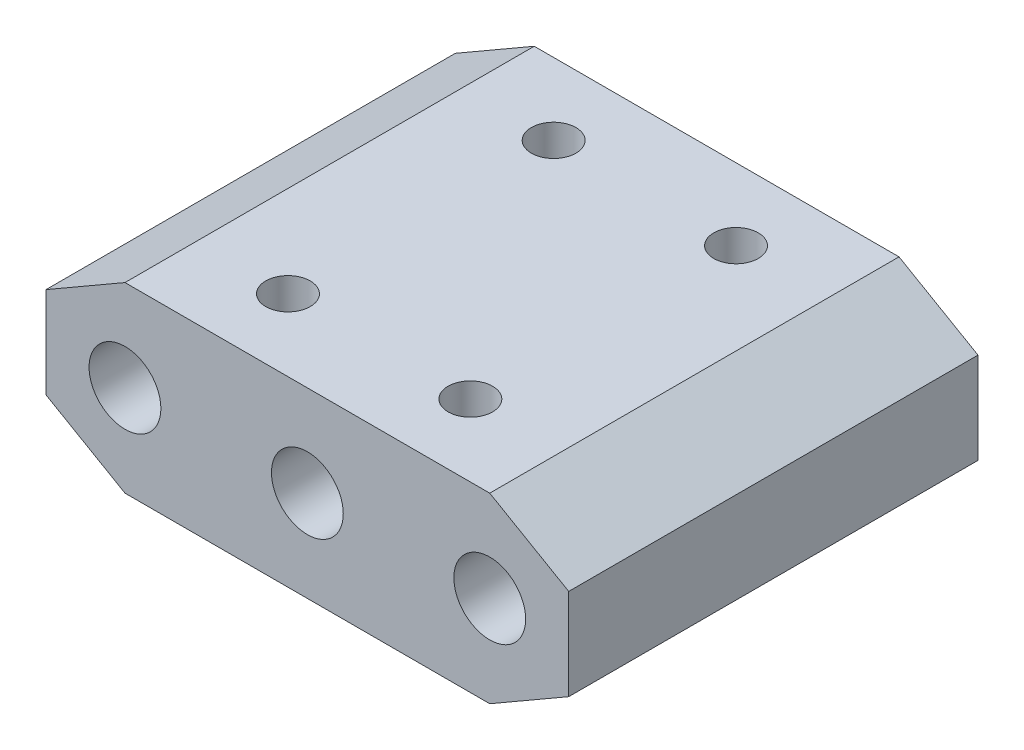
SolidWorks part; units mm, degrees
material "6061-T6 (SS)"
ref_plane "Front Plane" through (0, 0, 0) normal (0, 0, 1) x (1, 0, 0)
ref_plane "Top Plane" through (0, 0, 0) normal (0, 1, 0) x (1, 0, 0)
ref_plane "Right Plane" through (0, 0, 0) normal (1, 0, 0) x (0, 0, -1)
sketch "Sketch1" plane through (0, 0, 0) normal (0, 0, 1) x (1, 0, 0)
  line L0 (0, 6.35) -> (6.35, 6.35) construction
  line L1 (0, 0) -> (38.1, 0)
  line L2 (0, 0) -> (0, 12.7)
  line L3 (0, 12.7) -> (38.1, 12.7)
  line L4 (38.1, 0) -> (38.1, 12.7)
  line L5 (6.35, 6.35) -> (19.05, 6.35) construction
  line L6 (19.05, 6.35) -> (31.75, 6.35) construction
  line L7 (31.75, 6.35) -> (38.1, 6.35) construction
  line L9 (6.35, 0) -> (11.8493, 3.175)
  line L10 (11.8493, 3.175) -> (11.8493, 9.525)
  line L11 (11.8493, 9.525) -> (6.35, 12.7)
  line L12 (6.35, 12.7) -> (0.8507, 9.525)
  line L13 (0.8507, 9.525) -> (0.8507, 3.175)
  line L14 (0.8507, 3.175) -> (6.35, 0)
  line L15 (31.75, 0) -> (37.2493, 3.175)
  line L16 (37.2493, 3.175) -> (37.2493, 9.525)
  line L17 (37.2493, 9.525) -> (31.75, 12.7)
  line L18 (31.75, 12.7) -> (26.2507, 9.525)
  line L19 (26.2507, 9.525) -> (26.2507, 3.175)
  line L20 (26.2507, 3.175) -> (31.75, 0)
  circle A0 centre (6.35, 6.35) radius 5.4993 construction
  circle A1 centre (31.75, 6.35) radius 5.4993 construction
  dimension "D1" = 12.7
  dimension "D3" = 12.7
  dimension "D2" = 6.35
extrude "Boss-Extrude1" add sketch "Sketch1" against normal blind 28.5 contours L20 L19 L18 L3 L11 L10 L9 L1 | L13 L14 L9 L10 L11 L12 | L19 L20 L15 L16 L17 L18
hole_wizard "M6 Tapped Hole1" positions "Sketch2" profile "Sketch3" tap size "M6" standard "AS"
sketch "Sketch2" plane through (0, 0, 0) normal (0, 0, 1) x (1, 0, 0)
  point P2 (19.05, 6.35)
  point P4 (31.75, 6.35)
  point P11 (6.35, 6.35)
cosmetic thread "Hole Thread1" parameters "D1"=6, "D2"=6
cosmetic thread "Hole Thread2" parameters "D1"=6, "D2"=6
cosmetic thread "Hole Thread3" parameters "D1"=6, "D2"=6
sketch "Sketch3" plane through (19.05, 6.35, 0) normal (1, 0, 0) x (0, -1, 0)
  line L0 (0, 0) -> (0, 7.5022)
  line L1 (0, 7.5022) -> (2.5, 6)
  line L2 (2.5, 6) -> (2.5, 0)
  line L5 (2.5, 0) -> (0, 0)
  line L10 (0, 7.5022) -> (-2.5, 6) construction
  line L11 (0, -6.35) -> (0, 107.95) construction
  dimension "Tap Drill Dia." = 5
  dimension "Tap Drill Depth" = 6
  dimension "Drill Angle" = 118
hole_wizard "M6 Tapped Hole2" positions "Sketch7" profile "Sketch8" tap size "M6" standard "AS"
sketch "Sketch7" plane through (0, 0, -28.5) normal (0, 0, -1) x (-1, 0, 0)
  point P0 (-31.75, 6.35)
  point P3 (-19.05, 6.35)
  point P6 (-6.35, 6.35)
sketch "Sketch8" plane through (31.75, 6.35, -28.5) normal (1, 0, 0) x (0, 1, 0)
  line L0 (0, 0) -> (0, 9.5022)
  line L1 (0, 9.5022) -> (2.5, 8)
  line L2 (2.5, 8) -> (2.5, 0)
  line L5 (2.5, 0) -> (0, 0)
  line L10 (0, 9.5022) -> (-2.5, 8) construction
  line L11 (0, -6.35) -> (0, 107.95) construction
  dimension "Tap Drill Dia." = 5
  dimension "Tap Drill Depth" = 8
  dimension "Drill Angle" = 118
cosmetic thread "Hole Thread7" parameters "D1"=8, "D2"=6
cosmetic thread "Hole Thread8" parameters "D1"=8, "D2"=6
cosmetic thread "Hole Thread9" parameters "D1"=8, "D2"=6
sketch "Sketch6" plane through (0, 0, 0) normal (0, 0, 1) x (1, 0, 0)
  circle A0 centre (6.35, 6.35) radius 2.5
  circle A1 centre (19.05, 6.35) radius 2.5
  circle A2 centre (31.75, 6.35) radius 2.5
  dimension "D1" = 5
extrude "Cut-Extrude2" cut sketch "Sketch6" against normal through all
sketch "Sketch5" plane through (0, 12.7, 0) normal (0, 1, 0) x (1, 0, 0)
  line L0 (19.05, 23.5) -> (19.05, 28.5) construction
  line L1 (12.7, 23.5) -> (25.4, 23.5) construction
  line L2 (12.7, 23.5) -> (12.7, 5) construction
  line L3 (12.7, 5) -> (25.4, 5) construction
  line L4 (25.4, 23.5) -> (25.4, 5) construction
  line L5 (6.35, 28.5) -> (31.75, 28.5) construction
  line L6 (19.05, 5) -> (19.05, 0) construction
  line L7 (-6.985, 0) -> (6.985, 0) construction
  circle A0 centre (12.7, 23.5) radius 1.55
  circle A1 centre (25.4, 23.5) radius 1.55
  circle A2 centre (25.4, 5) radius 1.55
  circle A3 centre (12.7, 5) radius 1.55
  dimension "D3" = 3.1
  dimension "D1" = 12.7
  dimension "D2" = 5
extrude "Cut-Extrude1" cut sketch "Sketch5" against normal through all
equation "\"D3@Sketch1\"=\"D1@Sketch1\""
equation "\"D2@Sketch1\"=\"D1@Sketch1\"/2"
